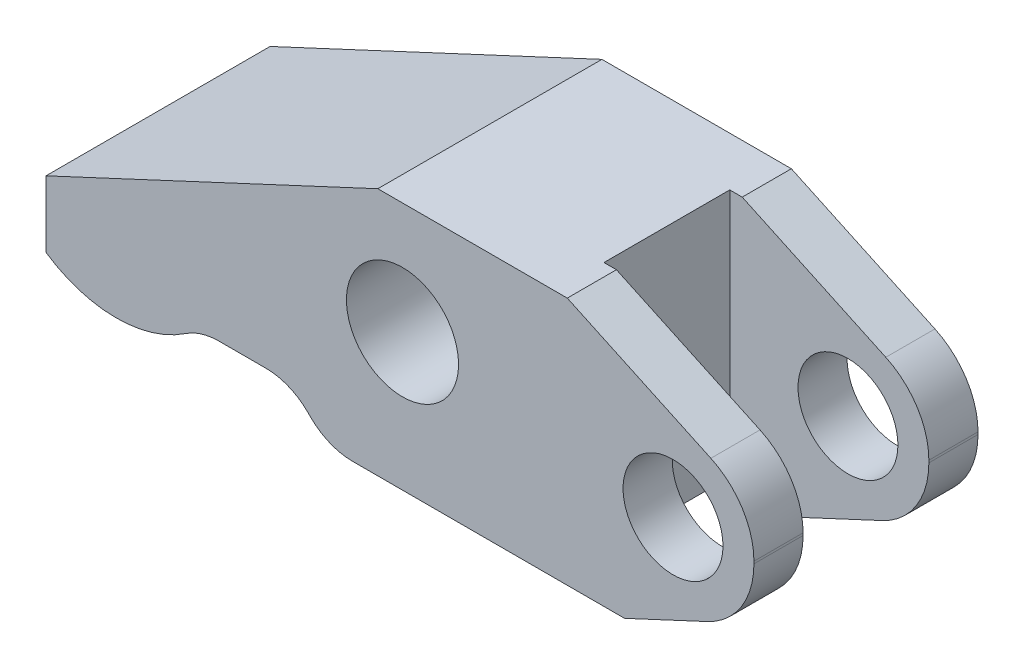
SolidWorks part; units mm, degrees
ref_plane "Front Plane" through (0, 0, 0) normal (0, 0, 1) x (1, 0, 0)
ref_plane "Top Plane" through (0, 0, 0) normal (0, 1, 0) x (1, 0, 0)
ref_plane "Right Plane" through (0, 0, 0) normal (1, 0, 0) x (0, 0, -1)
sketch "Sketch2" plane through (0, 0, 0) normal (0, 1, 0) x (1, 0, 0)
  line L0 (0, 0) -> (0, 26.0602) construction
  line L1 (0, 0) -> (34.3773, 0) construction
  line L3 (-28.448, 9.0043) -> (28.448, 9.0043)
  line L4 (-28.448, 9.0043) -> (-28.448, -9.0043)
  line L5 (-28.448, -9.0043) -> (28.448, -9.0043)
  line L6 (28.448, 9.0043) -> (28.448, -9.0043)
  point P10 (0, 9.0043)
  point P11 (28.448, 0)
  dimension "D1" = 56.896
  dimension "D2" = 18.0086
extrude "Boss-Extrude1" add sketch "Sketch2" along normal mid plane 19.9898
sketch "Sketch3" plane through (0, 0, 0) normal (0, 0, 1) x (1, 0, 0)
  line L0 (-28.448, -9.9949) -> (28.448, -9.9949) construction
  line L3 (28.448, 9.9949) -> (28.448, -9.9949) construction
  circle A0 centre (21.9456, -1.0033) radius 4.0157
  circle A1 centre (0.2032, 1.0033) radius 4.506
  dimension "D5" = 9.0119
  dimension "D6" = 8.0315
  dimension "D1" = 8.9916
  dimension "D2" = 6.5024
  dimension "D3" = 2.0066
  dimension "D4" = 21.7424
extrude "Cut-Extrude1" cut sketch "Sketch3" against normal through all and the other way through all
sketch "Sketch5" plane through (0, 0, 0) normal (0, 0, 1) x (1, 0, 0)
  line L0 (18.049, -9.9949) -> (24.6936, -6.8965)
  line L1 (-28.448, -9.9949) -> (28.448, -9.9949) construction
  line L2 (28.448, 9.9949) -> (28.448, -9.9949) construction
  line L3 (28.448, -1.0033) -> (28.448, -0.8186)
  line L4 (24.9869, 4.6142) -> (13.448, 9.9949)
  line L5 (-28.448, 9.9949) -> (28.448, 9.9949) construction
  line L6 (13.448, 9.9949) -> (-1.778, 9.9949)
  line L7 (-1.778, 9.9949) -> (-28.448, -2.4415)
  line L8 (-28.448, 9.9949) -> (-28.448, -9.9949) construction
  line L9 (-28.448, -2.4415) -> (-28.448, -9.9949)
  line L10 (-28.448, -9.9949) -> (18.049, -9.9949)
  arc A0 (28.448, -0.8186) -> (24.9869, 4.6142) centre (22.4536, -0.8186) ccw
  arc A1 (28.448, -1.0033) -> (24.6936, -6.8965) centre (21.9456, -1.0033) cw
  circle A2 centre (21.9456, -1.0033) radius 4.0157 construction
  point P18 (28.448, 3.0003)
  point P21 (28.448, -5.1458)
  dimension "D5" = 5.9944
  dimension "D6" = 15
  dimension "D1" = 25
  dimension "D2" = 25
  dimension "D3" = 26.67
  dimension "D4" = 25
extrude "Cut-Extrude2" cut sketch "Sketch5" against normal through all and the other way through all flip side to cut
sketch "Sketch6" plane through (0, 0, 0) normal (0, 0, 1) x (1, 0, 0)
  line L0 (-5.7912, -9.9949) -> (-8.7884, -6.9977)
  line L1 (-28.448, -9.9949) -> (18.049, -9.9949) construction
  line L2 (-8.7884, -6.9977) -> (-16.1754, -6.9977)
  line L3 (-22.8092, -9.5123) -> (-27.813, -9.5123) construction
  line L4 (28.448, -0.8186) -> (28.448, -1.0033) construction
  line L5 (-28.448, -7.7725) -> (-28.448, -9.9949)
  line L6 (-28.448, -2.4415) -> (-28.448, -9.9949) construction
  line L7 (-28.448, -9.9949) -> (-5.7912, -9.9949)
  arc A0 (-28.448, -7.7725) -> (-16.1754, -6.9977) centre (-22.8092, 0.4953) ccw
  circle A1 centre (0.2032, 1.0033) radius 4.506 construction
  circle A3 centre (21.9456, -1.0033) radius 4.0157 construction
  dimension "D2" = 10.0076
  dimension "D4" = 45
  dimension "D5" = 8.9916
  dimension "D6" = 8.001
  dimension "D1" = 8.509
  dimension "D3" = 51.2572
extrude "Cut-Extrude3" cut sketch "Sketch6" against normal through all and the other way through all
fillet "Fillet1" radius 4.7752 3 edges at (-16.1754, -6.9977, 0) (-8.7884, -6.9977, 0) (-5.7912, -9.9949, 0)
sketch "Sketch7" plane through (0, 0, 0) normal (0, 1, 0) x (1, 0, 0)
  line L0 (28.448, 9.0043) -> (28.448, -9.0043) construction
  line L1 (28.448, 5.0546) -> (12.446, 5.0546)
  line L2 (28.448, 5.0546) -> (28.448, -5.0546)
  line L3 (28.448, -5.0546) -> (12.446, -5.0546)
  line L4 (12.446, 5.0546) -> (12.446, -5.0546)
  line L5 (-10.9944, 0) -> (10.9944, 0) construction
  point P6 (28.448, 0)
  dimension "D1" = 10.1092
  dimension "D2" = 16.002
extrude "Cut-Extrude4" cut sketch "Sketch7" against normal through all and the other way through all
